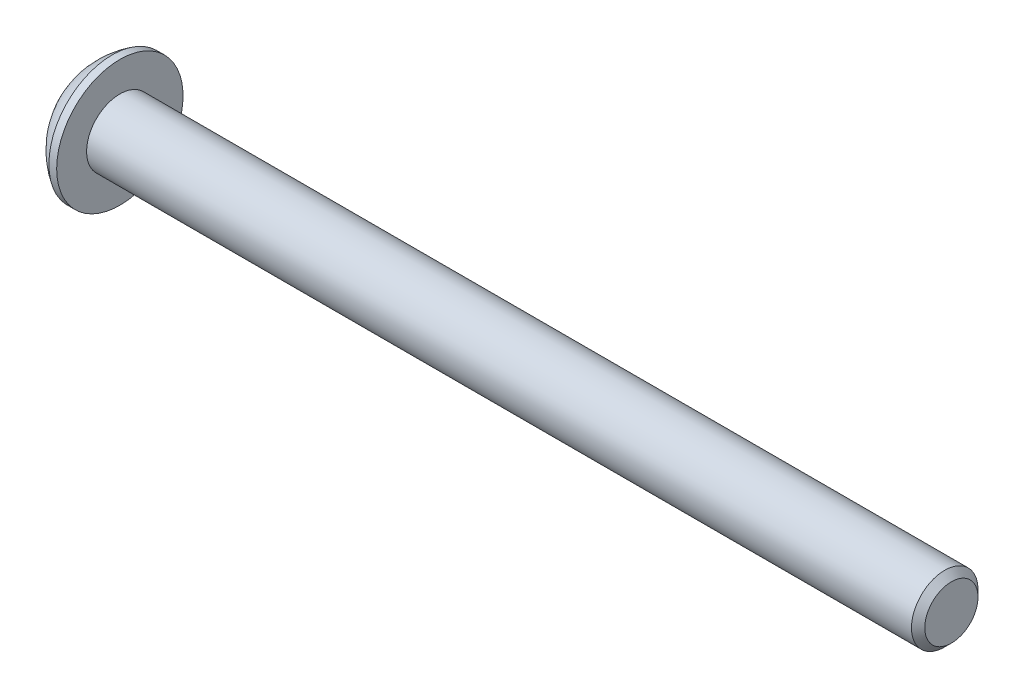
SolidWorks part; units mm, degrees
material "AISI 304"
ref_plane "Front Plane" through (0, 0, 0) normal (0, 0, 1) x (1, 0, 0)
ref_plane "Top Plane" through (0, 0, 0) normal (0, 1, 0) x (1, 0, 0)
ref_plane "Right Plane" through (0, 0, 0) normal (1, 0, 0) x (0, 0, -1)
sketch "Sketch2" plane through (0, 0, 0) normal (0, 0, 1) x (1, 0, 0)
  line L0 (0, 0) -> (39.15, 0)
  line L1 (39.15, 0) -> (39.15, 1.5)
  line L2 (39.15, 1.5) -> (1.65, 1.5)
  line L3 (1.65, 1.5) -> (1.65, 2.85)
  line L4 (0, 1.425) -> (0, 0)
  line L5 (1.65, 2.85) -> (1.3, 2.85)
  arc A1 (1.3, 2.85) -> (0, 1.425) centre (3.1356, -0.13) ccw
  dimension "D1" = 37.5
  dimension "D3" = 2.85
  dimension "D6" = 3.5
  dimension "D7" = 1.425
  dimension "D2" = 1.5
  dimension "D4" = 0.35
  dimension "D5" = 1.65
revolve "Revolve1" add sketch "Sketch2" angle 360 about L0
chamfer "Chamfer1" distance 0.3 angle 45 1 edges at (39.15, 0, 1.5)
sketch "Sketch3" plane through (0, 0, 0) normal (-1, 0, 0) x (0, 0, 1)
  line L7 (0.576, 1.0008) -> (-0.5787, 0.9992)
  line L8 (-0.5787, 0.9992) -> (-1.1547, -0.0015)
  line L9 (-1.1547, -0.0015) -> (-0.576, -1.0008)
  line L10 (-0.576, -1.0008) -> (0.5787, -0.9992)
  line L11 (0.5787, -0.9992) -> (1.1547, 0.0015)
  line L12 (1.1547, 0.0015) -> (0.576, 1.0008)
  circle A0 centre (0, 0) radius 1 construction
  dimension "D2" = 1.0008
  dimension "D1" = 2
extrude "Cut-Extrude1" cut sketch "Sketch3" against normal blind 1
